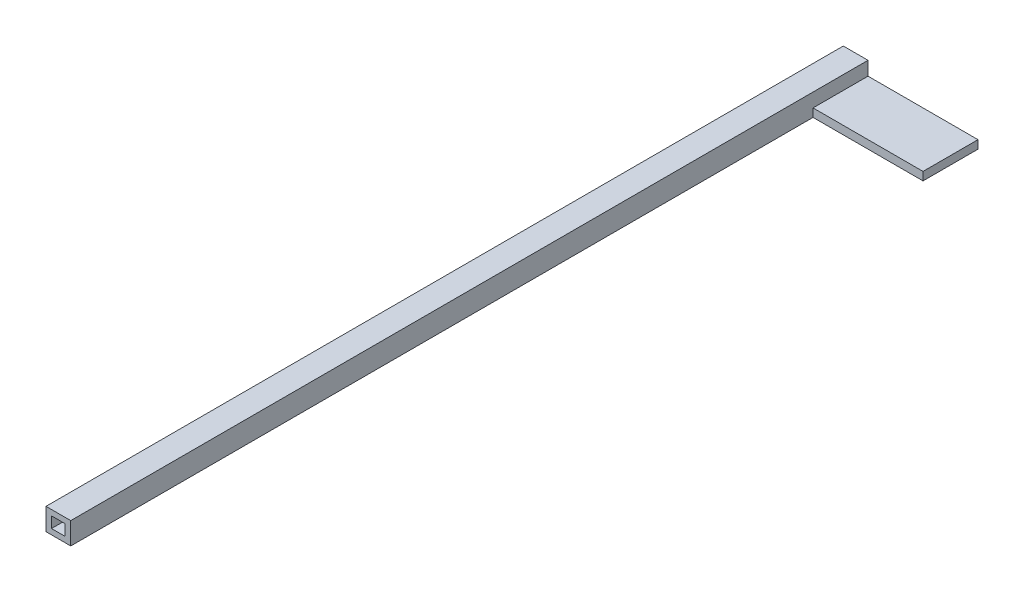
SolidWorks part; units mm, degrees
ref_plane "Front Plane" through (0, 0, 0) normal (0, 0, 1) x (1, 0, 0)
ref_plane "Top Plane" through (0, 0, 0) normal (0, 1, 0) x (1, 0, 0)
ref_plane "Right Plane" through (0, 0, 0) normal (1, 0, 0) x (0, 0, -1)
sketch "Sketch1" plane through (0, 0, 0) normal (0, 0, 1) x (1, 0, 0)
  line L1 (4.5, -4) -> (-4.5, -4)
  line L2 (4.5, -4) -> (4.5, 4)
  line L3 (4.5, 4) -> (-4.5, 4)
  line L4 (-4.5, -4) -> (-4.5, 4)
  line L5 (4.5, -4) -> (-4.5, 4) construction
  line L6 (4.5, 4) -> (-4.5, -4) construction
  point P1 (0, 0)
  dimension "D1" = 9
  dimension "D2" = 8
extrude "Boss-Extrude1" add sketch "Sketch1" along normal blind 290
sketch "Sketch2" plane through (4.5, 0, 0) normal (1, 0, 0) x (0, 0, -1)
  line L1 (0, -4) -> (-20, -4)
  line L2 (0, -4) -> (0, -1)
  line L3 (0, -1) -> (-20, -1)
  line L4 (-20, -4) -> (-20, -1)
  dimension "D1" = 20
  dimension "D2" = 3
extrude "Boss-Extrude2" add sketch "Sketch2" along normal blind 40
sketch "Sketch3" plane through (0, 0, 290) normal (0, 0, 1) x (1, 0, 0)
  line L0 (0, 4) -> (0, -4)
  line L1 (4.5, 4) -> (-4.5, 4) construction
  line L2 (-4.5, -4) -> (4.5, -4) construction
  line L4 (-2.5, -2) -> (2.5, -2)
  line L5 (-2.5, -2) -> (-2.5, 2)
  line L6 (-2.5, 2) -> (2.5, 2)
  line L7 (2.5, -2) -> (2.5, 2)
  line L8 (-2.5, -2) -> (2.5, 2) construction
  line L9 (-2.5, 2) -> (2.5, -2) construction
  point P6 (0, 0)
  dimension "D1" = 5
  dimension "D2" = 4
extrude "Cut-Extrude1" cut sketch "Sketch3" against normal blind 20 contours L6 L7 L4 L5
